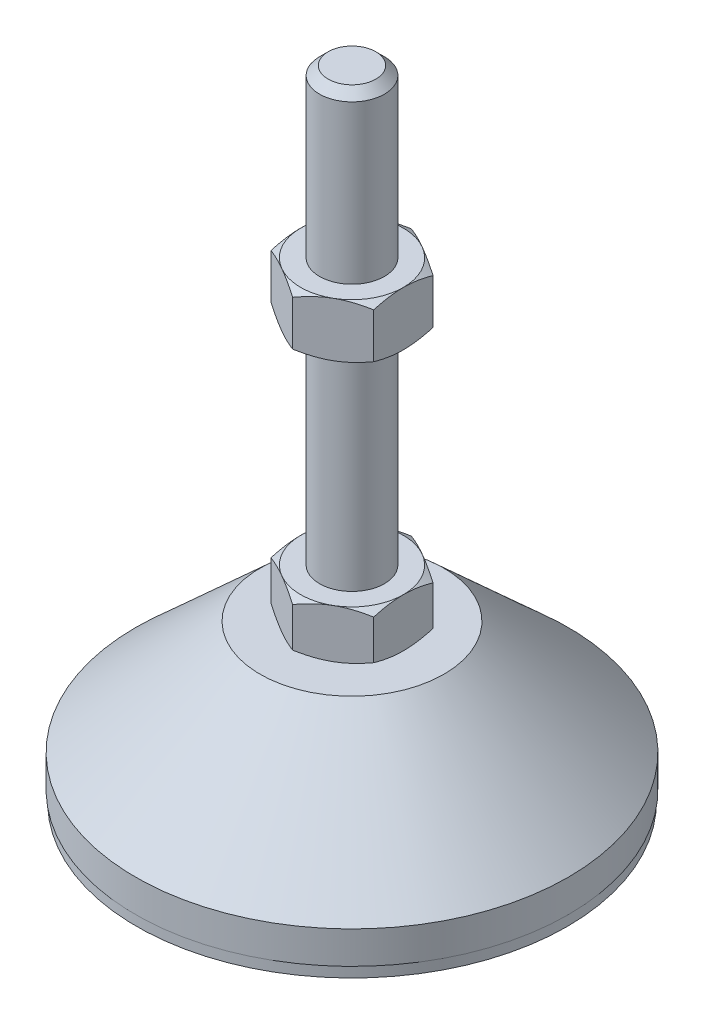
SolidWorks part; units mm, degrees
ref_plane "Спереди" through (0, 0, 0) normal (0, 0, 1) x (1, 0, 0)
ref_plane "Сверху" through (0, 0, 0) normal (0, 1, 0) x (1, 0, 0)
ref_plane "Справа" through (0, 0, 0) normal (1, 0, 0) x (0, 0, -1)
sketch "Эскиз1" plane through (0, 0, 0) normal (0, 0, 1) x (1, 0, 0)
  line L0 (0, 0) -> (-39.8, 0)
  line L1 (-39.8, 0) -> (-39.8, 2)
  line L2 (-39.8, 2) -> (-40, 2)
  line L3 (-40, 2) -> (-40, 8)
  line L4 (-40, 8) -> (-17, 29)
  line L5 (-17, 29) -> (-6, 29)
  line L12 (-6, 38) -> (-6, 116.4)
  line L13 (-6, 116.4) -> (-4.4, 118)
  line L14 (-4.4, 118) -> (0, 118)
  line L15 (0, 118) -> (0, 0) construction
  line L16 (-6, 29) -> (0, 29) construction
  line L17 (0, 0) -> (0, 118)
  line L18 (0, 0) -> (0, -7.9595) construction
  line L19 (-6, 38) -> (-6, 29)
  point P8 (-6, 77.2)
  point P23 (-11.5, 29)
  dimension "D1" = 12
  dimension "D2" = 29
  dimension "D3" = 9
  dimension "D4" = 80
  dimension "D5" = 6
  dimension "D6" = 1.6
  dimension "D7" = 45
  dimension "D8" = 34
  dimension "D9" = 2
  dimension "D10" = 80
  dimension "D11" = 6
  dimension "D12" = 0.2
revolve "Повернуть1" add sketch "Эскиз1" angle 360 about L17
sketch "Эскиз2" plane through (0, 29, 0) normal (0, 1, 0) x (1, 0, 0)
  line L1 (0, 10.9697) -> (-9.5, 5.4848)
  line L2 (-9.5, 5.4848) -> (-9.5, -5.4848)
  line L3 (-9.5, -5.4848) -> (0, -10.9697)
  line L4 (0, -10.9697) -> (9.5, -5.4848)
  line L5 (9.5, -5.4848) -> (9.5, 5.4848)
  line L6 (9.5, 5.4848) -> (0, 10.9697)
  circle A0 centre (0, 0) radius 9.5 construction
  dimension "D1" = 19
extrude "Бобышка-Вытянуть1" add sketch "Эскиз2" along normal up to vertex (9 mm away) up to point (-6, 38, 0)
ref_plane "Плоскость1" through (0, 77.2, 0) normal (0, 1, 0) x (1, 0, 0)
sketch "Эскиз3" plane through (0, 77.2, 0) normal (0, 1, 0) x (1, 0, 0)
  line L6 (9.5, 5.4848) -> (0, 10.9697)
  line L7 (0, 10.9697) -> (-9.5, 5.4848)
  line L8 (-9.5, 5.4848) -> (-9.5, -5.4848)
  line L9 (-9.5, -5.4848) -> (0, -10.9697)
  line L10 (0, -10.9697) -> (9.5, -5.4848)
  line L11 (9.5, -5.4848) -> (9.5, 5.4848)
  line L12 (9.5, 5.4848) -> (0, 10.9697)
  line L13 (0, 10.9697) -> (-9.5, 5.4848)
  line L14 (-9.5, 5.4848) -> (-9.5, -5.4848)
  line L15 (-9.5, -5.4848) -> (0, -10.9697)
  line L16 (0, -10.9697) -> (9.5, -5.4848)
  line L17 (9.5, -5.4848) -> (9.5, 5.4848)
  dimension "D1" = 0
extrude "Бобышка-Вытянуть2" add sketch "Эскиз3" along normal blind 10
sketch "Эскиз4" plane through (0, 0, 0) normal (0, 0, 1) x (1, 0, 0)
  line L0 (-9.5, 87.2) -> (-18.1603, 82.2)
  line L1 (-18.1603, 82.2) -> (-18.1603, 87.2)
  line L2 (-18.1603, 87.2) -> (-9.5, 87.2)
  line L3 (-18.1603, 82.2) -> (-9.5, 77.2)
  line L4 (50, 77.2) -> (-50, 77.2) construction
  line L5 (-9.5, 77.2) -> (-18.1603, 77.2)
  line L6 (-18.1603, 77.2) -> (-18.1603, 82.2)
  line L7 (-9.5, 87.2) -> (-9.5, 77.2) construction
  line L8 (-9.5, 38) -> (-17.2942, 38)
  line L9 (-17.2942, 38) -> (-17.2942, 33.5)
  line L10 (-17.2942, 33.5) -> (-9.5, 38)
  line L11 (-9.5, 29) -> (-17.2942, 33.5)
  line L12 (-17.2942, 33.5) -> (-17.2942, 29)
  line L13 (-17.2942, 29) -> (-9.5, 29)
  line L14 (0, 118) -> (0, 96.3793) construction
  dimension "D1" = 30
  dimension "D2" = 30
revolve "Вырез-Повернуть2" cut sketch "Эскиз4" angle 360 about L14
